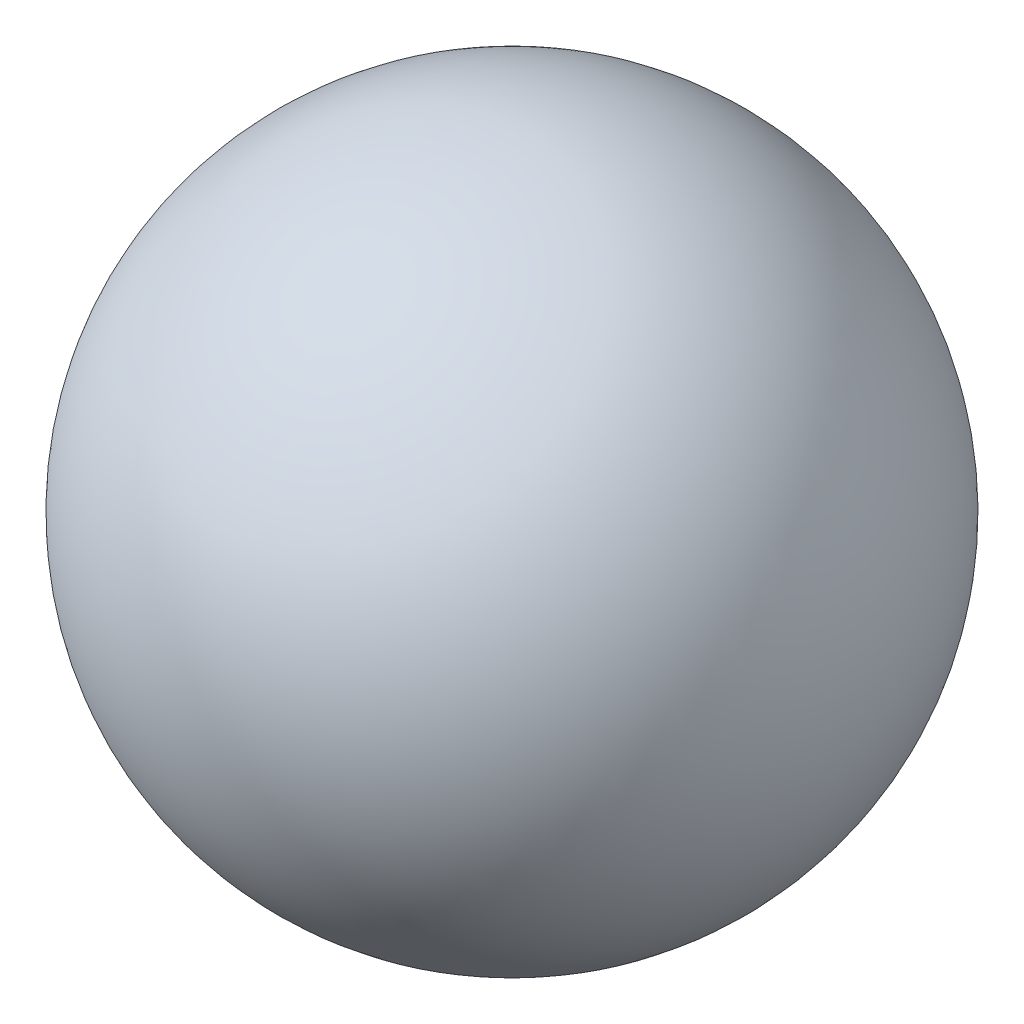
SolidWorks part; units mm, degrees
ref_plane "Vorne" through (0, 0, 0) normal (0, 0, 1) x (1, 0, 0)
ref_plane "Oben" through (0, 0, 0) normal (0, 1, 0) x (1, 0, 0)
ref_plane "Rechts" through (0, 0, 0) normal (1, 0, 0) x (0, 0, -1)
sketch "Skizze1" plane through (0, 0, 0) normal (0, 0, 1) x (1, 0, 0)
  line L0 (0, 35.6933) -> (0, -34.2144) construction
  line L1 (11, -16.7033) -> (3.3235, -16.7033)
  line L2 (0, 1.2937) -> (0, 20)
  line L3 (3.3235, -16.7033) -> (3.3235, -0.7033)
  line L4 (3.3235, -0.7033) -> (0, 1.2937)
  arc A0 (0, 20) -> (11, -16.7033) centre (0, 0) cw
  dimension "D1" = 20
  dimension "D2" = 22
  dimension "D3" = 36.7033
  dimension "D4" = 59
  dimension "D5" = 6.647
  dimension "D6" = 16
revolve "Rotation1" add sketch "Skizze1" angle 360 about L0
move or copy body "Körper-Verschieben/Kopieren1" [suppressed] bodies to move or copy 103
